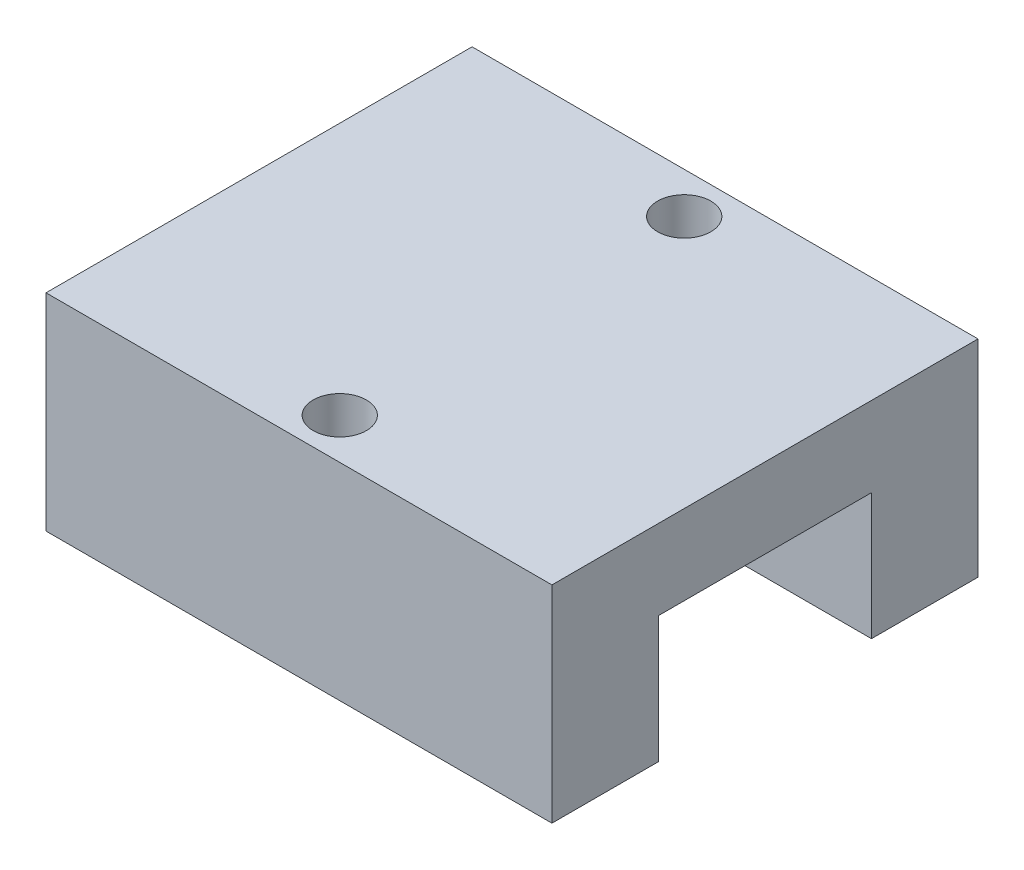
SolidWorks part; units mm, degrees
ref_plane "Front Plane" through (0, 0, 0) normal (0, 0, 1) x (1, 0, 0)
ref_plane "Top Plane" through (0, 0, 0) normal (0, 1, 0) x (1, 0, 0)
ref_plane "Right Plane" through (0, 0, 0) normal (1, 0, 0) x (0, 0, -1)
sketch "Sketch1" plane through (0, 0, 0) normal (0, 1, 0) x (1, 0, 0)
  line L0 (-9.5, -8) -> (9.5, 8) construction
  line L1 (-9.5, 8) -> (9.5, 8)
  line L2 (-9.5, 8) -> (-9.5, -8)
  line L3 (-9.5, -8) -> (9.5, -8)
  line L4 (9.5, 8) -> (9.5, -8)
  point P4 (0, 0)
  dimension "D1" = 19
  dimension "D2" = 16
extrude "Extrude1" add sketch "Sketch1" along normal blind 7.75
sketch "Sketch2" plane through (0, 0, 0) normal (0, -1, 0) x (1, 0, 0)
  circle A0 centre (0, -6.4675) radius 1 construction
  circle A1 centre (0, -6.4675) radius 1
  circle A2 centre (0, 6.4675) radius 1 construction
  circle A3 centre (0, 6.4675) radius 1
extrude "Cut-Extrude1" cut sketch "Sketch2" against normal blind 17.75
sketch "Sketch3" plane through (9.5, 0, 0) normal (1, 0, 0) x (0, 0, -1)
  line L0 (-8, 0) -> (8, 0) construction
  line L1 (-4, 0) -> (4, 0)
  line L2 (-4, 0) -> (-4, 4.75)
  line L3 (-4, 4.75) -> (4, 4.75)
  line L4 (4, 0) -> (4, 4.75)
  line L5 (-8, 7.75) -> (8, 7.75) construction
  line L6 (8, 7.75) -> (8, 0) construction
  line L7 (-8, 7.75) -> (-8, 0) construction
  dimension "D1" = 3
  dimension "D2" = 4
  dimension "D3" = 4
extrude "Cut-Extrude2" cut sketch "Sketch3" against normal blind 27.75
